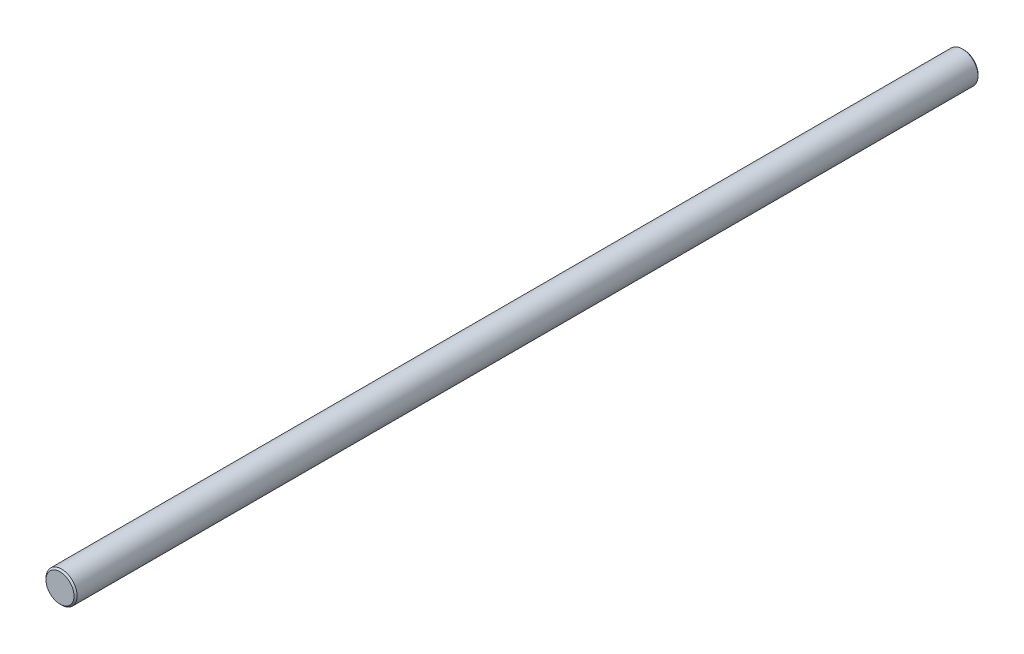
SolidWorks part; units mm, degrees
ref_plane "Plano frontal" through (0, 0, 0) normal (0, 0, 1) x (1, 0, 0)
ref_plane "Plano superior" through (0, 0, 0) normal (0, 1, 0) x (1, 0, 0)
ref_plane "Plano direito" through (0, 0, 0) normal (1, 0, 0) x (0, 0, -1)
sketch "Esboço1" plane through (0, 0, 0) normal (0, 0, 1) x (1, 0, 0)
  circle A0 centre (0, 0) radius 5
  dimension "D1" = 10
extrude "Ressalto-extrusão1" add sketch "Esboço1" along normal blind 290
chamfer "Chanfro1" distance 0.5 angle 45 2 edges at (5, 0, 290) (5, 0, 0)
